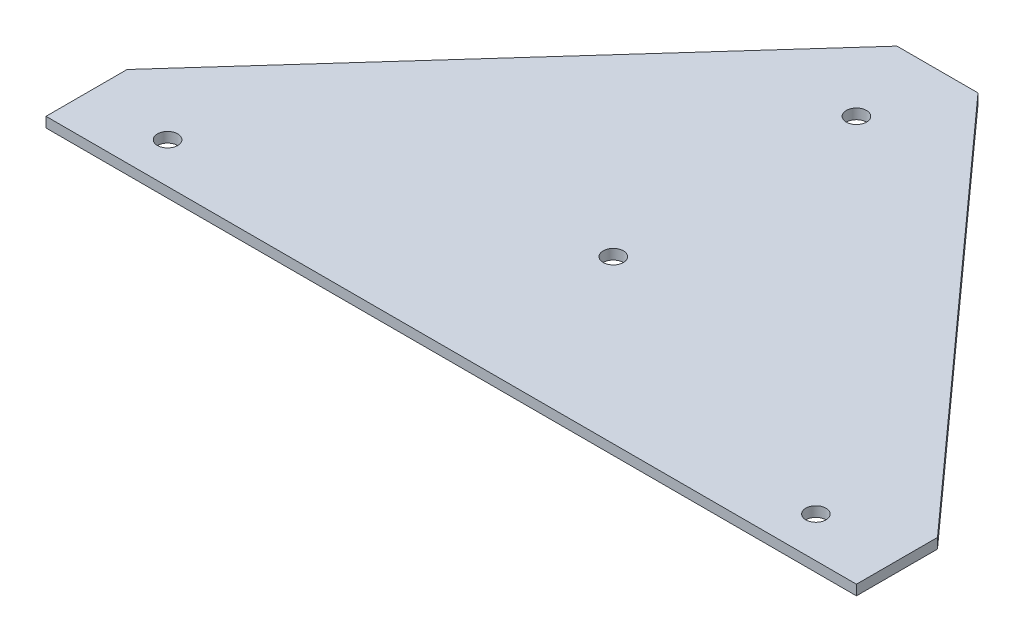
SolidWorks part; units mm, degrees
material "Pine"
ref_plane "Front Plane" through (0, 0, 0) normal (0, 0, 1) x (1, 0, 0)
ref_plane "Top Plane" through (0, 0, 0) normal (0, 1, 0) x (1, 0, 0)
ref_plane "Right Plane" through (0, 0, 0) normal (1, 0, 0) x (0, 0, -1)
sketch "Sketch1" plane through (0, 0, 0) normal (0, 1, 0) x (1, 0, 0)
  line L0 (127, 0) -> (-127, 0)
  line L1 (-127, 0) -> (-127, 25.4)
  line L2 (-127, 25.4) -> (-12.7, 152.4)
  line L3 (-12.7, 152.4) -> (12.7, 152.4)
  line L4 (0, 0) -> (0, 127) construction
  line L5 (127, 25.4) -> (12.7, 152.4)
  line L6 (127, 0) -> (127, 25.4)
  line L7 (-127, 12.7) -> (-101.6, 12.7) construction
  circle A0 centre (0, 127) radius 3.175
  circle A1 centre (0, 50.8) radius 3.175
  circle A2 centre (-101.6, 12.7) radius 3.175
  circle A3 centre (101.6, 12.7) radius 3.175
  point P10 (0, 152.4)
  dimension "D7" = 6.35
  dimension "D8" = 6.35
  dimension "D9" = 6.35
  dimension "D1" = 12.7
  dimension "D2" = 25.4
  dimension "D3" = 127
  dimension "D4" = 152.4
  dimension "D5" = 127
  dimension "D6" = 76.2
  dimension "D10" = 25.4
extrude "Boss-Extrude1" add sketch "Sketch1" along normal blind 3.175
